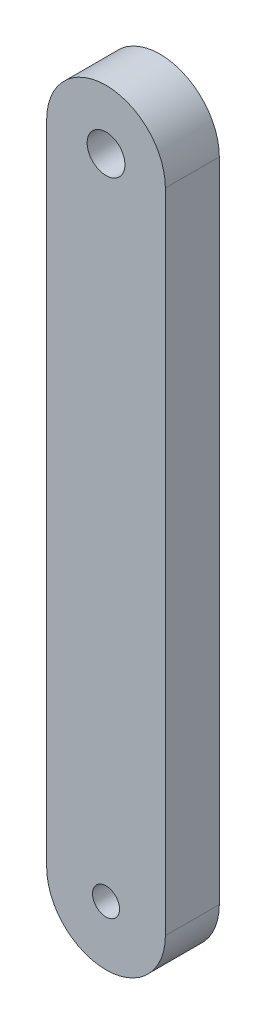
SolidWorks part; units mm, degrees
ref_plane "Front Plane" through (0, 0, 0) normal (0, 0, 1) x (1, 0, 0)
ref_plane "Top Plane" through (0, 0, 0) normal (0, 1, 0) x (1, 0, 0)
ref_plane "Right Plane" through (0, 0, 0) normal (1, 0, 0) x (0, 0, -1)
sketch "Sketch1" plane through (0, 0, 0) normal (0, 0, 1) x (1, 0, 0)
  line L3 (376.4095, 419.2441) -> (376.4095, 359.2441)
  line L4 (387.4095, 359.2441) -> (387.4095, 419.2441)
  arc A0 (387.4095, 419.2441) -> (376.4095, 419.2441) centre (381.9095, 419.2441) ccw
  circle A2 centre (381.9095, 419.2441) radius 1.75
  arc A3 (376.4095, 359.2441) -> (387.4095, 359.2441) centre (381.9095, 359.2441) ccw
  circle A4 centre (381.9095, 359.2441) radius 1.25
  dimension "D1" = 11
  dimension "D4" = 3.5
extrude "Boss-Extrude2" add sketch "Sketch1" along normal blind 5
